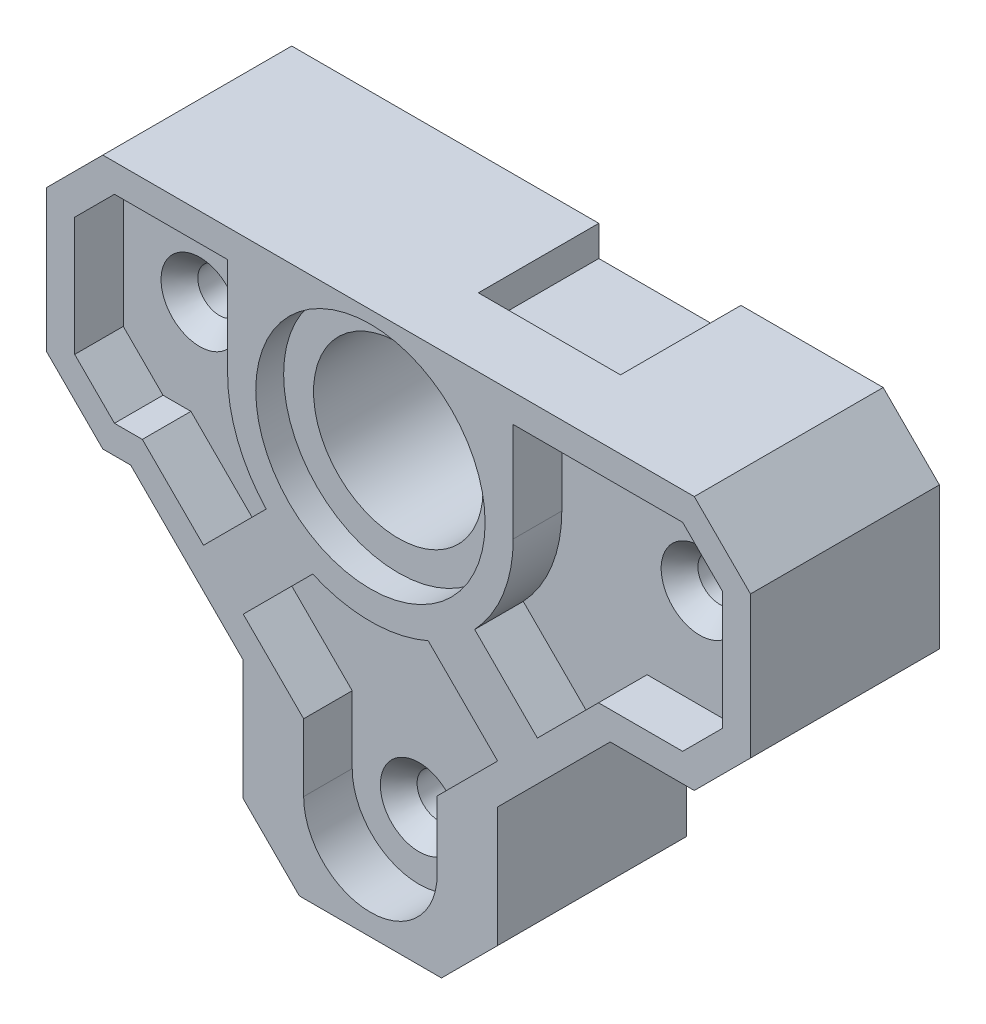
SolidWorks part; units mm, degrees
material "PET"
ref_plane "Front" through (0, 0, 0) normal (0, 0, 1) x (1, 0, 0)
ref_plane "Top" through (0, 0, 0) normal (0, 1, 0) x (1, 0, 0)
ref_plane "Right" through (0, 0, 0) normal (1, 0, 0) x (0, 0, -1)
sketch "Sketch1" plane through (0, 0, 0) normal (0, 0, 1) x (1, 0, 0)
  line L0 (-7.1882, -13.5382) -> (-7.1882, -23.495) construction
  line L1 (21.463, 7.1882) -> (-18.288, 7.1882)
  line L2 (21.463, 7.1882) -> (21.463, -7.1882)
  line L3 (21.463, -7.1882) -> (7.1882, -7.1882)
  line L4 (-18.288, 7.1882) -> (-18.288, -7.1882)
  line L5 (7.1882, -23.495) -> (-7.1882, -23.495)
  line L6 (7.1882, -23.495) -> (7.1882, -7.1882)
  line L8 (-7.1882, -23.495) -> (-7.1882, -7.1882)
  line L9 (-7.1882, -7.1882) -> (-18.288, -7.1882)
extrude "Boss-Extrude1" add sketch "Sketch1" along normal up to surface (10.668 mm away)
hole_wizard "CSK for #2 Flat Head Machine Screw1" positions "Sketch2" profile "Sketch3" countersink size "#2" standard "ANSI Inch" end condition through all
sketch "Sketch2" plane through (0, 0, 10.668) normal (0, 0, 1) x (1, 0, 0)
  line L0 (7.1882, -13.5382) -> (-7.1882, -13.5382) construction
  line L1 (7.1882, -7.1882) -> (7.1882, -23.495) construction
  line L2 (-7.1882, -23.495) -> (-7.1882, -7.1882) construction
  line L4 (0, -13.5382) -> (0, -23.495) construction
  line L5 (7.1882, -23.495) -> (-7.1882, -23.495) construction
  point P0 (15.8591, 0)
  point P3 (-12.3825, 0)
  point P7 (0, -18.5166)
sketch "Sketch3" plane through (15.8591, 0, 10.668) normal (1, 0, 0) x (0, -1, 0)
  line L0 (0, 0) -> (0, 10.668)
  line L1 (0, 10.668) -> (1.2192, 10.668)
  line L2 (1.2192, 10.668) -> (1.2192, 3.8535)
  line L3 (1.2192, 3.8535) -> (2.1844, 2.7432)
  line L4 (2.1844, 2.7432) -> (2.1844, 0)
  line L6 (2.1844, 0) -> (0, 0)
  line L7 (-1.2192, 3.8535) -> (-2.1844, 2.7432) construction
  line L11 (0, -6.35) -> (0, 107.95) construction
  dimension "Thru Hole Dia." = 2.4384
  dimension "Thru Hole Depth" = 10.668
  dimension "C'Sink Dia." = 4.3688
  dimension "C'Sink Angle" = 82
  dimension "Head Clearance" = 2.7432
sketch "Sketch4" plane through (0, 0, 10.668) normal (0, 0, 1) x (1, 0, 0)
  circle A0 centre (0, 0) radius 6.477
  dimension "D1" = 12.954
extrude "Cut-Extrude1" cut sketch "Sketch4" against normal blind 1.5748
sketch "Sketch5" plane through (0, 0, 10.668) normal (0, 0, 1) x (1, 0, 0)
  circle A0 centre (0, 0) radius 4.7879
  dimension "D1" = 9.5758
extrude "Cut-Extrude2" cut sketch "Sketch5" against normal through all
sketch "Sketch6" plane through (0, 0, 0) normal (0, 0, -1) x (-1, 0, 0)
  line L8 (-10.2553, 5.4667) -> (-2.2289, 5.4667)
  line L9 (-10.2553, 15.4997) -> (-10.2553, 5.4667)
  line L10 (-2.2289, 15.4997) -> (-10.2553, 15.4997)
  line L11 (-2.2289, 5.4667) -> (-2.2289, 15.4997)
  line L12 (-10.2553, 5.4667) -> (-2.2289, 5.4667)
  line L13 (-10.2553, 15.4997) -> (-10.2553, 5.4667)
  line L14 (-2.2289, 15.4997) -> (-10.2553, 15.4997)
  line L15 (-2.2289, 5.4667) -> (-2.2289, 15.4997)
  dimension "D1" = 0.762
extrude "Cut-Extrude3" cut sketch "Sketch6" against normal blind 5.08
draft "Draft2" type of draft neutral plane draft angle 45 faces to draft 1 face at (6.2421, 6.3275, 5.08) neutral plane through (10.2553, 5.4667, 5.08) neutral plane normal (0, 1, 0) parameters "D1"=45
chamfer "Chamfer1" distance 3.175 angle 45 6 edges at (-18.288, 7.1882, 5.334) (21.463, 7.1882, 5.334) (21.463, -7.1882, 5.334) (7.1882, -23.495, 5.334) (-7.1882, -23.495, 5.334) (-18.288, -7.1882, 5.334)
chamfer "Chamfer2" distance 6.35 angle 45 2 edges at (-7.1882, -7.1882, 5.334) (7.1882, -7.1882, 5.334)
sketch "Sketch7" plane through (0, 0, 10.668) normal (0, 0, 1) x (1, 0, 0)
  line L3 (3.7719, -14.7094) -> (7.1831, -11.2982)
  line L4 (12.8806, -5.6007) -> (17.6304, -5.6007)
  line L5 (17.6304, -5.6007) -> (19.8755, -3.3556)
  line L6 (19.8755, -3.3556) -> (19.8755, 3.3556)
  line L7 (19.8755, 3.3556) -> (17.6304, 5.6007)
  line L8 (17.6304, 5.6007) -> (8.0645, 5.6007)
  line L9 (-14.4554, 5.6007) -> (-16.7005, 3.3556)
  line L10 (-16.7005, 3.3556) -> (-16.7005, -3.3556)
  line L11 (-16.7005, -3.3556) -> (-14.4554, -5.6007)
  line L12 (-14.4554, -5.6007) -> (-12.8806, -5.6007)
  line L13 (-12.8806, -5.6007) -> (-9.4282, -9.0531)
  line L16 (-4.0132, -23.495) -> (4.0132, -23.495)
  line L17 (4.0132, -23.495) -> (7.1882, -20.32)
  line L18 (7.1882, -20.32) -> (7.1882, -13.5382)
  line L19 (7.1882, -13.5382) -> (13.5382, -7.1882)
  line L20 (13.5382, -7.1882) -> (18.288, -7.1882)
  line L21 (18.288, -7.1882) -> (21.463, -4.0132)
  line L22 (21.463, -4.0132) -> (21.463, 4.0132)
  line L23 (21.463, 4.0132) -> (18.288, 7.1882)
  line L24 (18.288, 7.1882) -> (-15.113, 7.1882)
  line L25 (-15.113, 7.1882) -> (-18.288, 4.0132)
  line L26 (-18.288, 4.0132) -> (-18.288, -4.0132)
  line L27 (-18.288, -4.0132) -> (-15.113, -7.1882)
  line L28 (-15.113, -7.1882) -> (-13.5382, -7.1882)
  line L29 (-13.5382, -7.1882) -> (-7.1882, -13.5382)
  line L30 (-7.1882, -13.5382) -> (-7.1882, -20.32)
  line L31 (-7.1882, -20.32) -> (-4.0132, -23.495)
  line L32 (-4.0132, -23.495) -> (4.0132, -23.495) construction
  line L33 (4.0132, -23.495) -> (7.1882, -20.32) construction
  line L34 (7.1882, -20.32) -> (7.1882, -13.5382) construction
  line L35 (7.1882, -13.5382) -> (13.5382, -7.1882) construction
  line L36 (13.5382, -7.1882) -> (18.288, -7.1882) construction
  line L37 (18.288, -7.1882) -> (21.463, -4.0132) construction
  line L38 (21.463, -4.0132) -> (21.463, 4.0132) construction
  line L39 (21.463, 4.0132) -> (18.288, 7.1882) construction
  line L40 (18.288, 7.1882) -> (-15.113, 7.1882) construction
  line L41 (-15.113, 7.1882) -> (-18.288, 4.0132) construction
  line L42 (-18.288, 4.0132) -> (-18.288, -4.0132) construction
  line L43 (-18.288, -4.0132) -> (-15.113, -7.1882) construction
  line L44 (-15.113, -7.1882) -> (-13.5382, -7.1882) construction
  line L45 (-13.5382, -7.1882) -> (-7.1882, -13.5382) construction
  line L46 (-7.1882, -13.5382) -> (-7.1882, -20.32) construction
  line L47 (-7.1882, -20.32) -> (-4.0132, -23.495) construction
  line L48 (-8.0645, 5.6007) -> (-14.4554, 5.6007)
  line L49 (17.6304, 5.6007) -> (-14.4554, 5.6007) construction
  line L50 (5.6007, -19.6624) -> (5.6007, -12.8806) construction
  line L51 (-5.6007, -12.8806) -> (-5.6007, -19.6624) construction
  line L52 (-5.6007, -19.6624) -> (-3.3556, -21.9075) construction
  line L53 (-3.3556, -21.9075) -> (3.3556, -21.9075) construction
  line L54 (3.3556, -21.9075) -> (5.6007, -19.6624) construction
  line L55 (3.7719, -18.5166) -> (3.7719, -14.7094)
  line L56 (5.6007, -12.8806) -> (12.8806, -5.6007) construction
  line L57 (-3.7719, -18.5166) -> (-3.7719, -14.7094)
  line L58 (-12.8806, -5.6007) -> (-5.6007, -12.8806) construction
  line L59 (8.0645, 0) -> (8.0645, 5.6007)
  line L60 (-8.0645, 0) -> (-8.0645, 5.6007)
  line L61 (9.4282, -11.2982) -> (4.6903, -6.5603) construction
  line L62 (9.4282, -9.0531) -> (5.8869, -5.5118)
  line L63 (7.1831, -11.2982) -> (3.2608, -7.3759)
  line L64 (9.4282, -9.0531) -> (5.8128, -5.4378) construction
  line L65 (7.1831, -11.2982) -> (3.5678, -7.6828) construction
  line L66 (0, 0) -> (0, -23.495) construction
  line L67 (-9.4282, -9.0531) -> (-5.8869, -5.5118)
  line L68 (-7.1831, -11.2982) -> (-3.2608, -7.3759)
  line L69 (9.4282, -9.0531) -> (12.8806, -5.6007)
  line L70 (8.3057, -10.1757) -> (4.6903, -6.5603) construction
  line L71 (-7.1831, -11.2982) -> (-3.7719, -14.7094)
  arc A0 (5.8869, -5.5118) -> (8.0645, 0) centre (0, 0) ccw
  arc A1 (-3.2608, -7.3759) -> (3.2608, -7.3759) centre (0, 0) ccw
  circle A2 centre (0, 0) radius 8.0645
  arc A3 (-8.0645, 0) -> (-5.8869, -5.5118) centre (0, 0) ccw
  circle A8 centre (0, -18.5166) radius 3.7719
  arc A9 (-3.7719, -18.5166) -> (3.7719, -18.5166) centre (0, -18.5166) ccw
  dimension "D5" = 1.5875
  dimension "D1" = 0
  dimension "D2" = 1.5875
  dimension "D3" = 1.5875
  dimension "D4" = 1.5875
  dimension "D6" = 1.5875
extrude "Cut-Extrude4" cut sketch "Sketch7" against normal blind 2.7432
